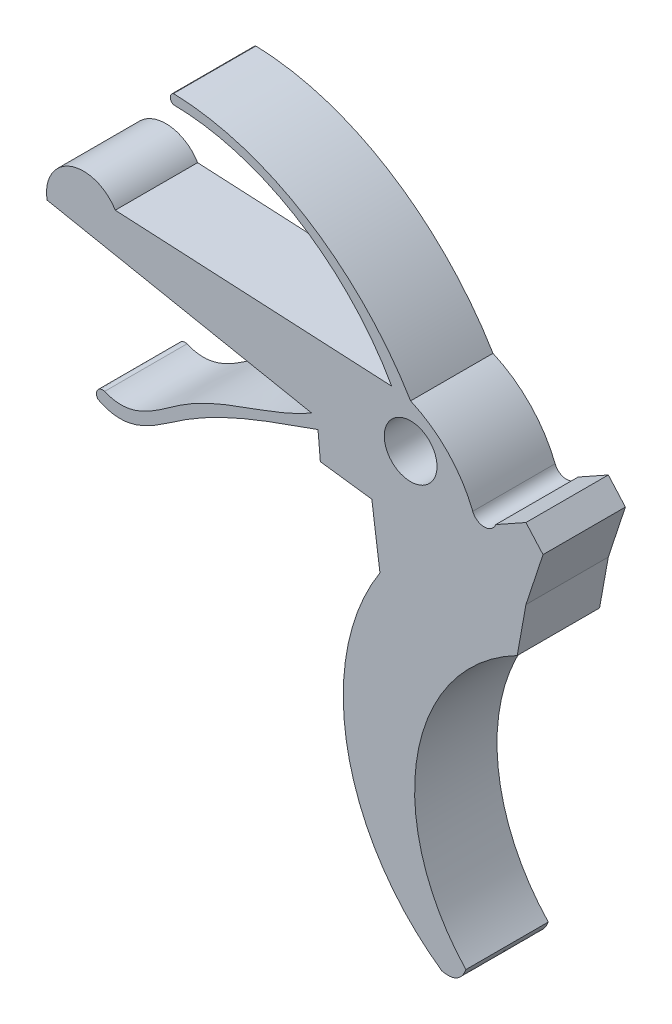
SolidWorks part; units mm, degrees
ref_plane "Plan de face" through (0, 0, 0) normal (0, 0, 1) x (1, 0, 0)
ref_plane "Plan de dessus" through (0, 0, 0) normal (0, 1, 0) x (1, 0, 0)
ref_plane "Plan de droite" through (0, 0, 0) normal (1, 0, 0) x (0, 0, -1)
sketch "Esquisse1" plane through (0, 0, 0) normal (0, 0, 1) x (1, 0, 0)
  line L0 (39.6415, 20.6139) -> (39.6415, 5.6139) construction
  line L1 (22.3272, 31.3796) -> (39.1104, 30.5197)
  line L2 (18.1932, 29.8414) -> (34.2535, 26.6786)
  line L3 (34.6368, 26.0047) -> (34.7774, 24.3854)
  line L4 (34.7774, 24.3854) -> (37.902, 23.9768)
  line L5 (37.902, 23.9768) -> (38.3952, 20.3484)
  line L6 (48.2943, 26.2597) -> (47.2574, 23.1121)
  line L7 (47.2574, 23.1121) -> (46.7269, 20.1693)
  line L8 (45.4249, 26.4032) -> (47.2574, 27.4288)
  line L9 (47.2574, 27.4288) -> (48.2943, 26.2597)
  line L10 (30.9805, 42.3618) -> (31.6064, 37.4011) construction
  arc A0 (22.3272, 31.3796) -> (18.1932, 29.8414) centre (20.4014, 30.2309) ccw
  circle A1 centre (40.2574, 27.6739) radius 1.6
  arc A2 (46.7269, 20.1693) -> (43.6124, 2.1046) centre (51.9794, 9.9629) ccw
  arc A3 (38.3952, 20.3484) -> (42.1533, 1.3062) centre (50.1541, 12.7771) ccw
  arc A4 (44.0294, 26.4032) -> (40.2574, 30.3221) centre (37.3818, 23.7796) ccw
  arc A5 (44.0294, 26.4032) -> (45.4249, 26.4032) centre (44.7271, 26.6786) ccw
  arc A6 (21.6844, 21.5349) -> (21.2795, 20.9179) centre (21.5658, 21.1714) ccw
  arc A7 (25.8602, 39.2785) -> (25.8602, 38.6928) centre (25.9867, 38.9857) ccw
  spline S0 degree 2 poles (42.1533, 1.3062) (43.2161, 1.0581) (43.6124, 2.1046) knots 0 0 0 1 1 1
  spline S1 degree 3 poles (34.6368, 26.0047) (31.6672, 24.9415) (27.3105, 23.5249) (23.1726, 19.9221) (21.2795, 20.9179) knots 0 0 0 0 0.624835 1 1 1 1
  spline S2 degree 3 poles (34.2535, 26.6786) (31.6638, 25.1921) (27.283, 24.6025) (23.4719, 20.7845) (21.6844, 21.5349) knots 0 0 0 0 0.618455 1 1 1 1
  spline S3 degree 3 poles (39.1104, 30.5197) (36.4704, 35.234) (31.3638, 38.6342) (25.8602, 38.6928) knots 0 0 0 0 1 1 1 1
  spline S4 degree 3 poles (40.2574, 30.3221) (37.2546, 35.3387) (31.8348, 39.118) (25.8602, 39.2785) knots 0 0 0 0 1 1 1 1
  dimension "D1" = 15
extrude "Boss.-Extru.1" add sketch "Esquisse1" along normal blind 5
